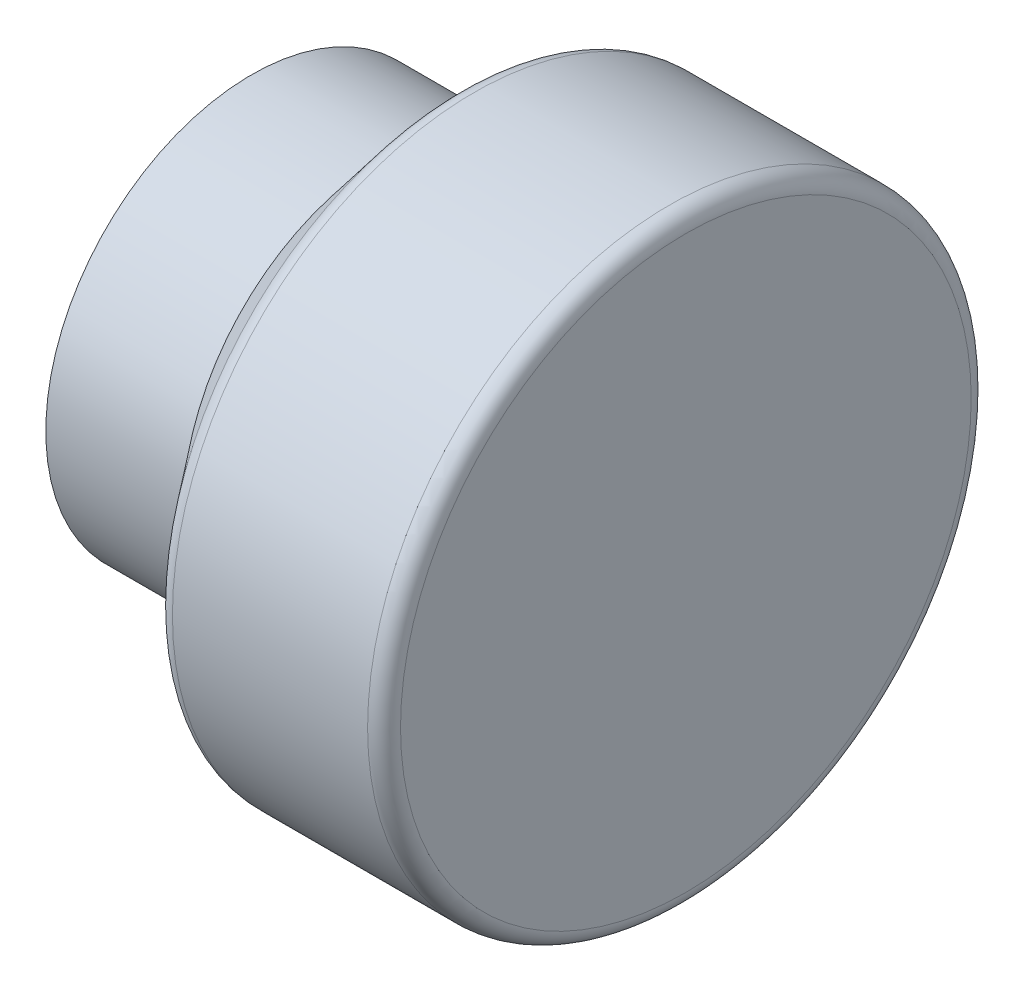
SolidWorks part; units mm, degrees
ref_plane "Front Plane" through (0, 0, 0) normal (0, 0, 1) x (1, 0, 0)
ref_plane "Top Plane" through (0, 0, 0) normal (0, 1, 0) x (1, 0, 0)
ref_plane "Right Plane" through (0, 0, 0) normal (1, 0, 0) x (0, 0, -1)
sketch "Sketch1" plane through (0, 0, 0) normal (0, 1, 0) x (1, 0, 0)
  line L0 (-37.0292, 17.4625) -> (-37.0292, 19.05)
  line L1 (-37.0292, 19.05) -> (-24.3292, 19.05)
  line L2 (-24.3292, 19.05) -> (-17.145, 27.94)
  line L3 (-17.145, 27.94) -> (3.175, 27.94)
  line L4 (3.175, 27.94) -> (3.175, 0)
  line L5 (3.175, 0) -> (0, 0)
  line L6 (0, 0) -> (0, 24.765)
  line L7 (0, 24.765) -> (-15.6286, 24.765)
  line L8 (-15.6286, 24.765) -> (-22.8128, 15.875)
  line L9 (-22.8128, 15.875) -> (-35.429, 15.875)
  line L10 (-35.429, 15.875) -> (-35.429, 17.4625)
  line L11 (-35.429, 17.4625) -> (-37.0292, 17.4625)
  point P2 (0, 0)
  point P14 (4.3312, 0)
  dimension "D1" = 27.94
  dimension "D2" = 20.32
  dimension "D3" = 12.7
  dimension "D4" = 1.6002
  dimension "D5" = 3.175
  dimension "D6" = 3.175
  dimension "D7" = 3.175
  dimension "D8" = 3.175
  dimension "D9" = 17.4625
  dimension "D10" = 15.875
  dimension "D11" = 11.43
revolve "Revolve1" add sketch "Sketch1" angle 360 about L5
fillet "Fillet1" radius 1.524 2 edges at (3.175, 0, -27.94) (-17.145, 0, -27.94)
